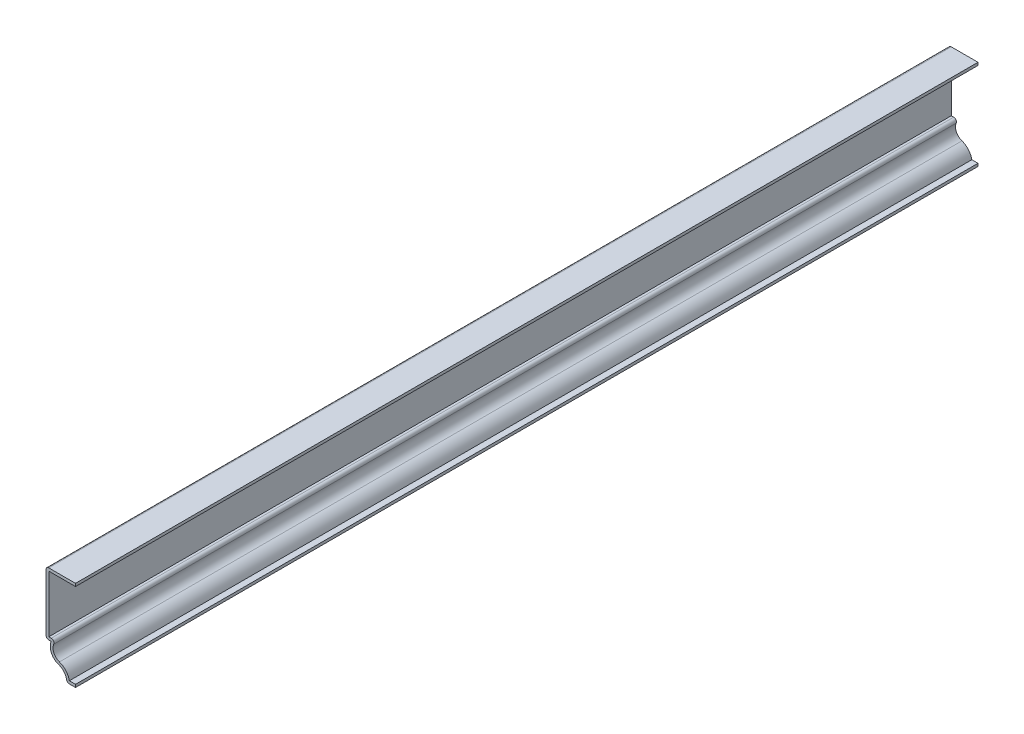
SolidWorks part; units mm, degrees
ref_plane "Front Plane" through (0, 0, 0) normal (0, 0, 1) x (1, 0, 0)
ref_plane "Top Plane" through (0, 0, 0) normal (0, 1, 0) x (1, 0, 0)
ref_plane "Right Plane" through (0, 0, 0) normal (1, 0, 0) x (0, 0, -1)
sketch "Sketch1" plane through (0, 0, 0) normal (0, 0, 1) x (1, 0, 0)
  line L0 (0, 0) -> (-3.9688, 0)
  line L1 (-11.1125, 12.7) -> (-13.4937, 12.7)
  line L2 (-13.4937, 12.7) -> (-13.4937, 41.275)
  line L3 (-13.4937, 41.275) -> (0, 41.275)
  arc A0 (-3.9688, 0) -> (-7.7598, 5.2684) centre (-9.525, 0) ccw
  arc A1 (-7.7598, 5.2684) -> (-11.1125, 12.7) centre (-5.9946, 10.5368) cw
  point P10 (0, 0)
  point P11 (-18.7657, 4.8214)
  point P12 (-13.8363, 12.7)
  point P13 (0, 0)
  dimension "D4" = 5.5562
  dimension "D1" = 41.275
  dimension "D2" = 28.575
  dimension "D3" = 2.3813
  dimension "D5" = 3.9688
  dimension "D6" = 13.4937
extrude "Extrude-Thin1" add sketch "Sketch1" against normal blind 412.75 thin
fillet "Fillet1" radius 1.27 4 edges at (-3.9688, 0, -206.375) (-8.5608, 13.97, -206.375) (-13.4937, 12.7, -206.375) (-13.4937, 41.275, -206.375)
